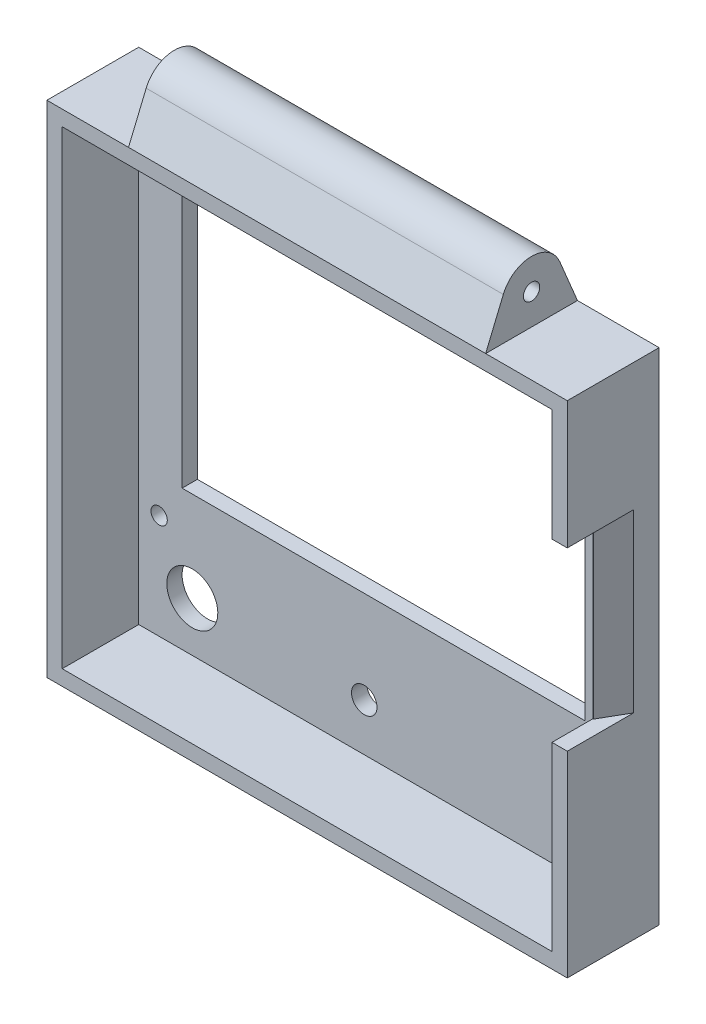
SolidWorks part; units mm, degrees
material "ABS"
ref_plane "Plano frontal" through (0, 0, 0) normal (0, 0, 1) x (1, 0, 0)
ref_plane "Plano superior" through (0, 0, 0) normal (0, 1, 0) x (1, 0, 0)
ref_plane "Plano direito" through (0, 0, 0) normal (1, 0, 0) x (0, 0, -1)
sketch "Esboço2" plane through (0, 0, 0) normal (1, 0, 0) x (0, 0, -1)
  line L0 (0, 0) -> (18, 0)
  line L2 (18, 0) -> (18, 98)
  line L3 (18, 98) -> (0, 98)
  line L4 (0, 98) -> (0, 0)
  dimension "D1" = 98
  dimension "D3" = 18
extrude "Ressalto-extrusão1" add sketch "Esboço2" along normal mid plane 102
shell "Casca1" thickness 3
sketch "Esboço4" plane through (0, 0, -18) normal (0, 0, -1) x (1, 0, 0)
  line L0 (51, -98) -> (-51, -98) construction
  line L1 (39.5, -82) -> (-39.5, -82)
  line L2 (39.5, -82) -> (39.5, -30.4)
  line L3 (39.5, -30.4) -> (-39.5, -30.4)
  line L4 (-39.5, -82) -> (-39.5, -30.4)
  line L5 (39.5, -82) -> (-39.5, -30.4) construction
  line L6 (39.5, -30.4) -> (-39.5, -82) construction
  line L8 (44, -23.5) -> (-44, -23.5) construction
  line L9 (44, -23.5) -> (44, -88.5) construction
  line L10 (44, -88.5) -> (-44, -88.5) construction
  line L11 (-44, -23.5) -> (-44, -88.5) construction
  line L12 (44, -23.5) -> (-44, -88.5) construction
  line L13 (44, -88.5) -> (-44, -23.5) construction
  circle A0 centre (-44, -23.5) radius 1.6
  circle A1 centre (-44, -88.5) radius 1.6
  circle A2 centre (44, -88.5) radius 1.6
  circle A3 centre (44, -23.5) radius 1.6
  circle A4 centre (-37.5, -12.7) radius 5
  circle A5 centre (36.75, -15.3) radius 3
  circle A6 centre (-3.8, -12.3) radius 2.5
  point P0 (0, -56.2)
  point P9 (0, -56)
  dimension "D7" = 3.2
  dimension "D11" = 10
  dimension "D14" = 6
  dimension "D16" = 5
  dimension "D1" = 51.6
  dimension "D2" = 79
  dimension "D3" = 16
  dimension "D4" = 65
  dimension "D5" = 88
  dimension "D6" = 6.5
  dimension "D8" = 75.8
  dimension "D9" = 6.5
  dimension "D10" = 7.25
  dimension "D12" = 76.2
  dimension "D13" = 40.2
  dimension "D15" = 8.2
extrude "Corte-extrusão1" cut sketch "Esboço4" against normal up to surface (3 mm away) up to face at (0, 49, -15)
sketch "Esboço5" plane through (51, 0, 0) normal (1, 0, 0) x (0, 0, -1)
  line L0 (14.5385, 106.3077) -> (18, 98)
  line L1 (18, 98) -> (0, 98)
  line L2 (0, 98) -> (3.4615, 106.3077)
  arc A0 (14.5385, 106.3077) -> (3.4615, 106.3077) centre (9, 104) ccw
  circle A1 centre (9, 104) radius 1.6
  point P9 (9, 98)
  dimension "D1" = 12
  dimension "D2" = 3.2
extrude "Ressalto-extrusão2" add sketch "Esboço5" against normal through all
sketch "Esboço6" plane through (0, 0, -18) normal (0, 0, -1) x (-1, 0, 0)
  line L0 (-51, 98) -> (51, 98) construction
  line L1 (-35, 110) -> (35, 110) construction
  line L2 (-35, 98) -> (-35, 110)
  line L3 (35, 98) -> (51, 98)
  line L4 (35, 98) -> (35, 110)
  line L5 (35, 110) -> (51, 110)
  line L6 (-51, 98) -> (-35, 98)
  line L7 (-51, 98) -> (-51, 110)
  line L8 (-51, 110) -> (-35, 110)
  line L9 (51, 98) -> (51, 110)
  line L10 (51, 110) -> (-51, 110) construction
  line L11 (51, 0) -> (51, 98) construction
  point P6 (0, 110)
  point P8 (0, 98)
  dimension "D1" = 70
extrude "Corte-extrusão2" cut sketch "Esboço6" against normal through all
sketch "Esboço7" plane through (51, 0, 0) normal (1, 0, 0) x (0, 0, -1)
  line L0 (0, 98) -> (18, 98) construction
  line L1 (0, 73) -> (8, 73)
  line L2 (0, 73) -> (0, 38.5)
  line L3 (0, 38.5) -> (8, 38.5)
  line L4 (8, 73) -> (8, 38.5)
  line L5 (0, 98) -> (0, 0) construction
  dimension "D1" = 25
  dimension "D2" = 34.5
  dimension "D3" = 8
extrude "Corte-extrusão3" cut sketch "Esboço7" against normal blind 10
chamfer "Chanfro1" distance 5 angle 30 1 edges at (51, 55.75, -8)
